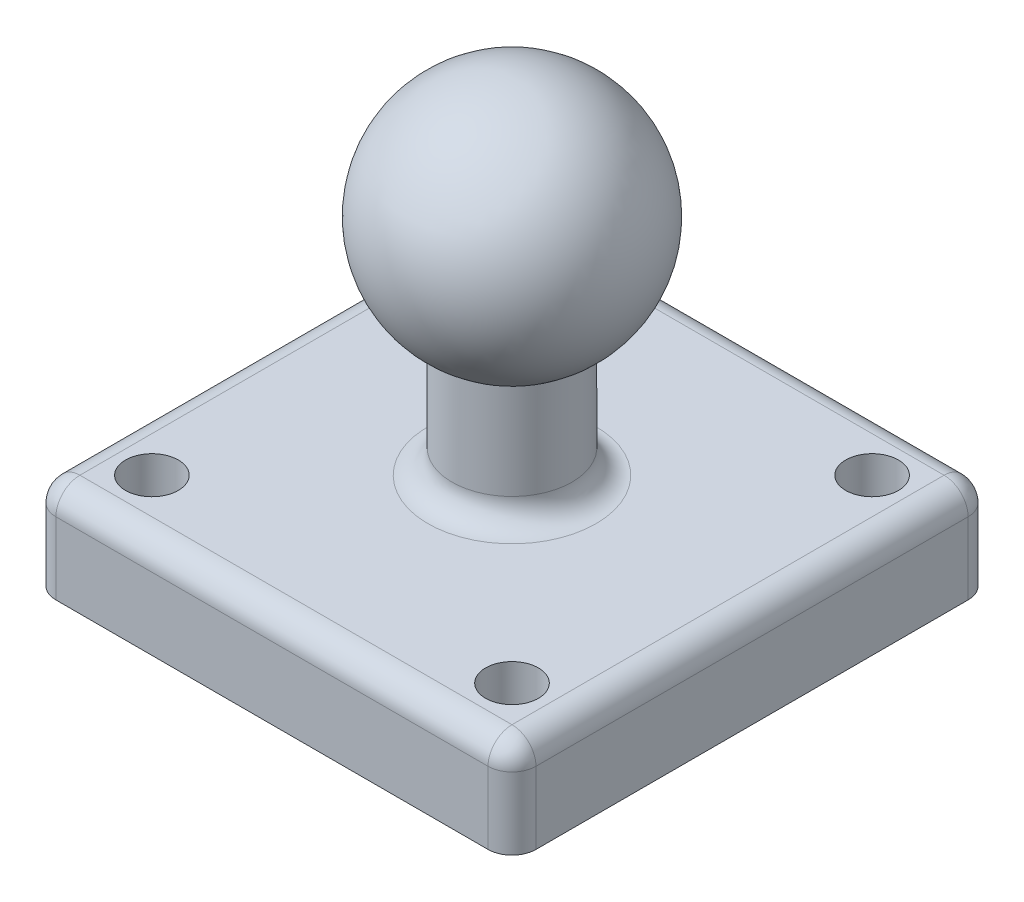
SolidWorks part; units mm, degrees
ref_plane "Plan de face" through (0, 0, 0) normal (0, 0, 1) x (1, 0, 0)
ref_plane "Plan de dessus" through (0, 0, 0) normal (0, 1, 0) x (1, 0, 0)
ref_plane "Plan de droite" through (0, 0, 0) normal (1, 0, 0) x (0, 0, -1)
sketch "Esquisse1" plane through (0, 0, 0) normal (0, 0, 1) x (1, 0, 0)
  line L0 (-2.5, -4.3301) -> (-2.5, -9.3301)
  line L1 (-2.5, -9.3301) -> (0, -9.3301)
  line L2 (0, -9.3301) -> (0, 5)
  line L3 (0, 5) -> (-7.2649, 5) construction
  arc A0 (0, 5) -> (-2.5, -4.3301) centre (0, 0) ccw
  dimension "D1" = 5
  dimension "D2" = 5
  dimension "D3" = 2.5
revolve "Révolution1" add sketch "Esquisse1" angle 360 about L2
sketch "Esquisse2" plane through (0, -9.3301, 0) normal (0, -1, 0) x (1, 0, 0)
  line L1 (-10, 10) -> (10, 10)
  line L2 (-10, 10) -> (-10, -10)
  line L3 (-10, -10) -> (10, -10)
  line L4 (10, 10) -> (10, -10)
  circle A0 centre (0, 0) radius 2.5 construction
  dimension "D3" = 10
  dimension "D4" = 10
  dimension "D1" = 20
  dimension "D2" = 20
extrude "Boss.-Extru.1" add sketch "Esquisse2" along normal blind 4
sketch "Esquisse3" plane through (0, -9.3301, 0) normal (0, 1, 0) x (1, 0, 0)
  circle A0 centre (7.5, -7.5) radius 1.1
  circle A1 centre (7.5, 7.5) radius 1.1
  circle A2 centre (-7.5, 7.5) radius 1.1
  circle A3 centre (-7.5, -7.5) radius 1.1
  circle A4 centre (0, 0) radius 2.5 construction
  dimension "D1" = 2.2
  dimension "D2" = 15
  dimension "D3" = 15
  dimension "D4" = 7.5
  dimension "D5" = 7.5
extrude "Enlèv. mat.-Extru.1" cut sketch "Esquisse3" against normal up to next
fillet "Congé1" radius 1 9 edges at (-10, -11.3301, -10) (2.5, -9.3301, 0) (-10, -9.3301, 0) (0, -9.3301, -10) (10, -11.3301, -10) (10, -11.3301, 10) (0, -9.3301, 10) (10, -9.3301, 0) (-10, -11.3301, 10)
